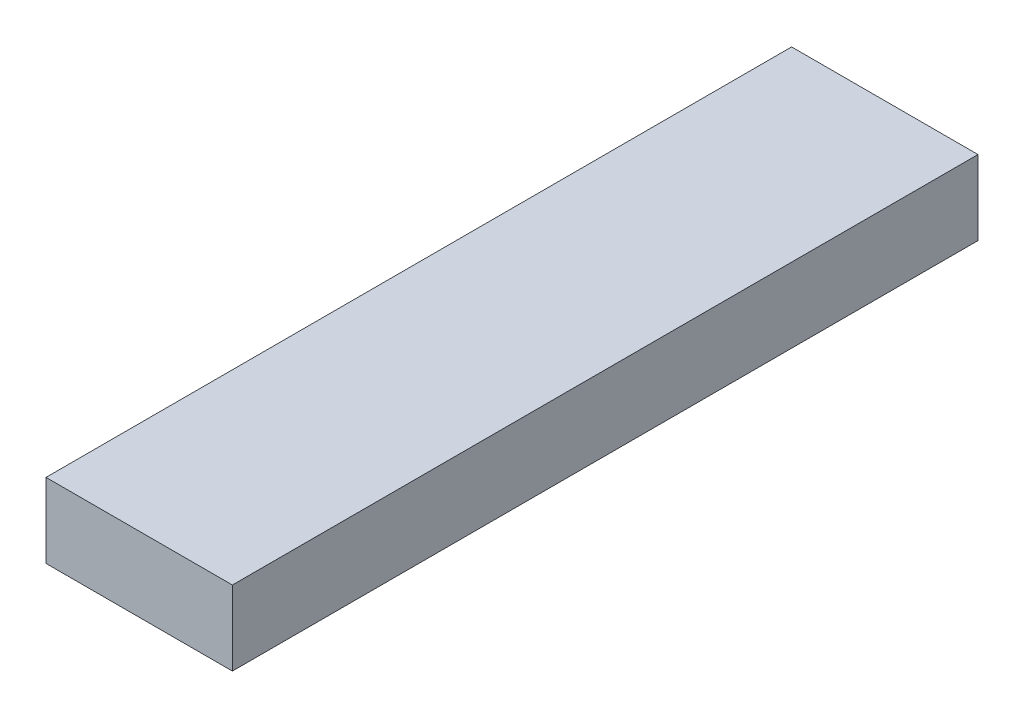
SolidWorks part; units mm, degrees
ref_plane "前视基准面" through (0, 0, 0) normal (0, 0, 1) x (1, 0, 0)
ref_plane "上视基准面" through (0, 0, 0) normal (0, 1, 0) x (1, 0, 0)
ref_plane "右视基准面" through (0, 0, 0) normal (1, 0, 0) x (0, 0, -1)
other "Configuration Table"
sketch "草图1" plane through (0, 0, 0) normal (0, 1, 0) x (1, 0, 0)
  line L0 (0, 0) -> (0, -200)
  line L1 (0, -200) -> (50, -200)
  line L2 (50, -200) -> (50, 0)
  line L3 (50, 0) -> (0, 0)
  dimension "D1" = 200
  dimension "D2" = 50
extrude "凸台-拉伸1" add sketch "草图1" along normal mid plane 20
